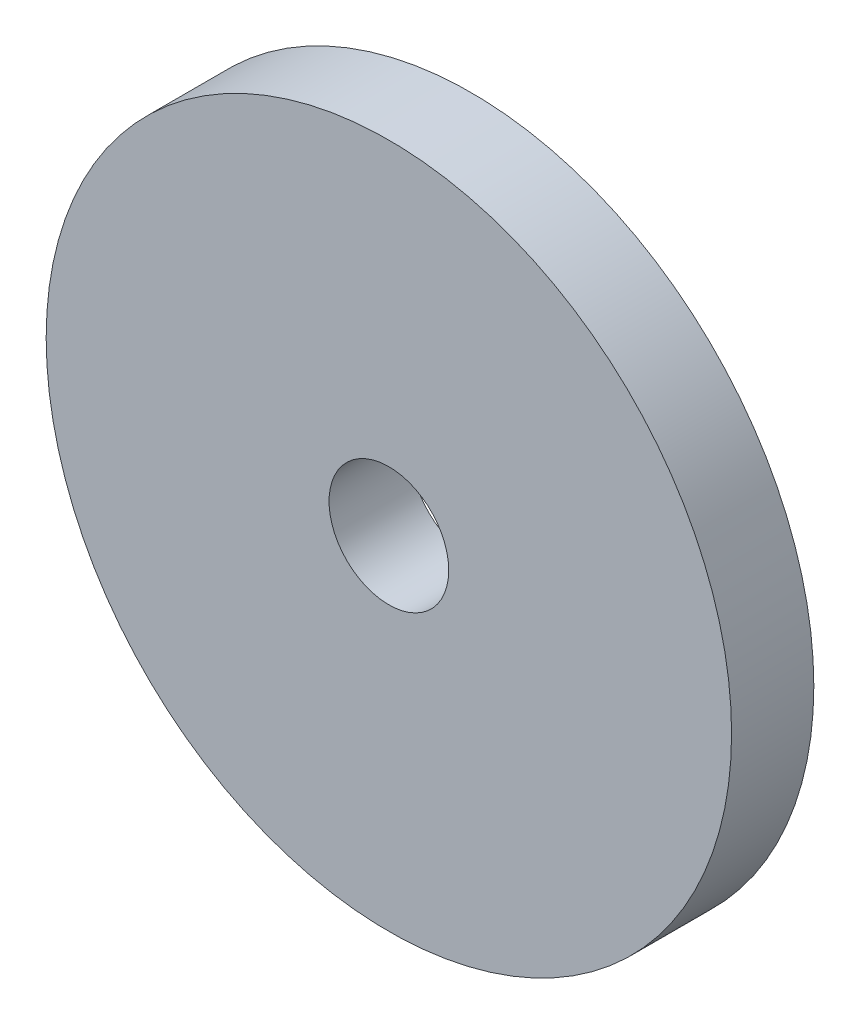
SolidWorks part; units mm, degrees
ref_plane "Front Plane" through (0, 0, 0) normal (0, 0, 1) x (1, 0, 0)
ref_plane "Top Plane" through (0, 0, 0) normal (0, 1, 0) x (1, 0, 0)
ref_plane "Right Plane" through (0, 0, 0) normal (1, 0, 0) x (0, 0, -1)
sketch "Sketch1" plane through (0, 0, 0) normal (0, 0, 1) x (1, 0, 0)
  circle A0 centre (0, 0) radius 31.75
  circle A3 centre (0, 0) radius 5.5433
extrude "Boss-Extrude1" add sketch "Sketch1" along normal blind 7.62
